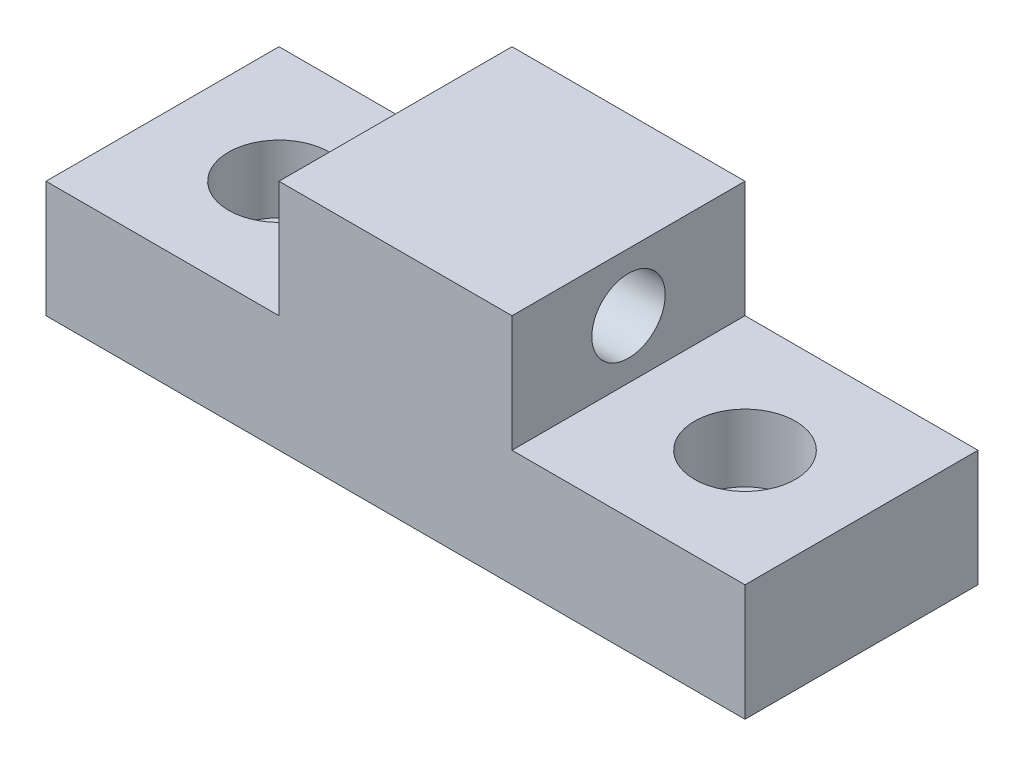
SolidWorks part; units mm, degrees
material "Bambu PAHT-CF"
ref_plane "Front Plane" through (0, 0, 0) normal (0, 0, 1) x (1, 0, 0)
ref_plane "Top Plane" through (0, 0, 0) normal (0, 1, 0) x (1, 0, 0)
ref_plane "Right Plane" through (0, 0, 0) normal (1, 0, 0) x (0, 0, -1)
sketch "Sketch1" plane through (0, 0, 0) normal (0, 1, 0) x (1, 0, 0)
  line L0 (-25.4, 0) -> (0, 0) construction
  line L1 (-38.1, -12.7) -> (38.1, -12.7)
  line L2 (-38.1, -12.7) -> (-38.1, 12.7)
  line L3 (-38.1, 12.7) -> (38.1, 12.7)
  line L4 (38.1, -12.7) -> (38.1, 12.7)
  line L5 (-38.1, -12.7) -> (38.1, 12.7) construction
  line L6 (-38.1, 12.7) -> (38.1, -12.7) construction
  line L7 (-25.4, 0) -> (-38.1, 0) construction
  line L8 (-38.1, -12.7) -> (-12.7, -12.7)
  line L9 (-38.1, -12.7) -> (-38.1, 12.7)
  line L10 (-38.1, 12.7) -> (-12.7, 12.7)
  line L11 (-12.7, -12.7) -> (-12.7, 12.7) construction
  line L12 (-25.4, 0) -> (-12.7, 0) construction
  line L13 (0, -12.7) -> (0, 12.7) construction
  circle A0 centre (-25.4, 0) radius 3.5012
  circle A1 centre (25.4, 0) radius 3.5012
  point P0 (0, 0)
  dimension "D3" = 7.0024
  dimension "D1" = 25.4
  dimension "D2" = 76.2
  dimension "D4" = 25.4
extrude "Boss-Extrude1" add sketch "Sketch1" along normal blind 12.7 contours L1 L4 L3 L2 A0 A1
sketch "Sketch2" plane through (0, 12.7, 0) normal (0, 1, 0) x (1, 0, 0)
  line L0 (-38.1, 12.7) -> (38.1, 12.7) construction
  line L1 (-12.7, -12.7) -> (12.7, -12.7)
  line L2 (-12.7, -12.7) -> (-12.7, 12.7)
  line L3 (-12.7, 12.7) -> (12.7, 12.7)
  line L4 (12.7, -12.7) -> (12.7, 12.7)
  line L5 (-12.7, -12.7) -> (12.7, 12.7) construction
  line L6 (-12.7, 12.7) -> (12.7, -12.7) construction
  point P0 (0, 0)
  dimension "D1" = 25.4
extrude "Boss-Extrude2" add sketch "Sketch2" along normal blind 12.7
sketch "Sketch3" plane through (-12.7, 0, 0) normal (-1, 0, 0) x (0, 0, 1)
  line L0 (-12.7, 12.7) -> (12.7, 25.4) construction
  line L1 (12.7, 25.4) -> (12.7, 12.7) construction
  line L2 (12.7, 12.7) -> (-12.7, 25.4) construction
  line L3 (-12.7, 25.4) -> (-12.7, 12.7) construction
  circle A0 centre (0, 19.05) radius 4.0012
  dimension "D1" = 8.0024
extrude "Cut-Extrude1" cut sketch "Sketch3" against normal blind 43.7
sketch "Sketch4" plane through (0, 12.7, 0) normal (0, 1, 0) x (1, 0, 0)
  circle A0 centre (-25.4, 0) radius 5.5
  circle A1 centre (25.4, 0) radius 5.5
  dimension "D1" = 11
  dimension "D2" = 11
  dimension "D3" = 25.4
  dimension "D4" = 25.4
extrude "Cut-Extrude2" cut sketch "Sketch4" against normal blind 7.35
sketch "Sketch5" plane through (-38.1, 0, 0) normal (-1, 0, 0) x (0, 0, 1)
  line L0 (12.7, 0) -> (-12.7, 0) construction
  line L1 (-3.2512, 0) -> (3.2512, 0)
  line L2 (-3.2512, 0) -> (-3.2512, -2)
  line L3 (-1.2512, -4) -> (1.2512, -4)
  line L4 (3.2512, 0) -> (3.2512, -2)
  line L5 (-12.7, 0) -> (-3.2512, 0) construction
  line L6 (3.2512, 0) -> (12.7, 0) construction
  line L7 (-3.2512, -2) -> (-1.2512, -4)
  line L8 (1.2512, -4) -> (3.2512, -2)
  point P1 (3.2512, -4)
  point P2 (-3.2512, -4)
  line M4 (-12.7, 0) -> (12.7, 0)
  dimension "D1" = 6.5024
  dimension "D2" = 4
extrude "Boss-Extrude3" [suppressed] add sketch "Sketch5" against normal up to vertex contours L3 L8 L4 L2 L7 M4
sketch "Sketch6" plane through (0, 5.35, 0) normal (0, 1, 0) x (1, 0, 0)
  circle A0 centre (25.4, 0) radius 3.5012 construction
  circle A1 centre (-25.4, 0) radius 3.5012 construction
  circle A2 centre (25.4, 0) radius 3.5012
  circle A3 centre (-25.4, 0) radius 3.5012
extrude "Cut-Extrude3" [suppressed] cut sketch "Sketch6" against normal blind 86
